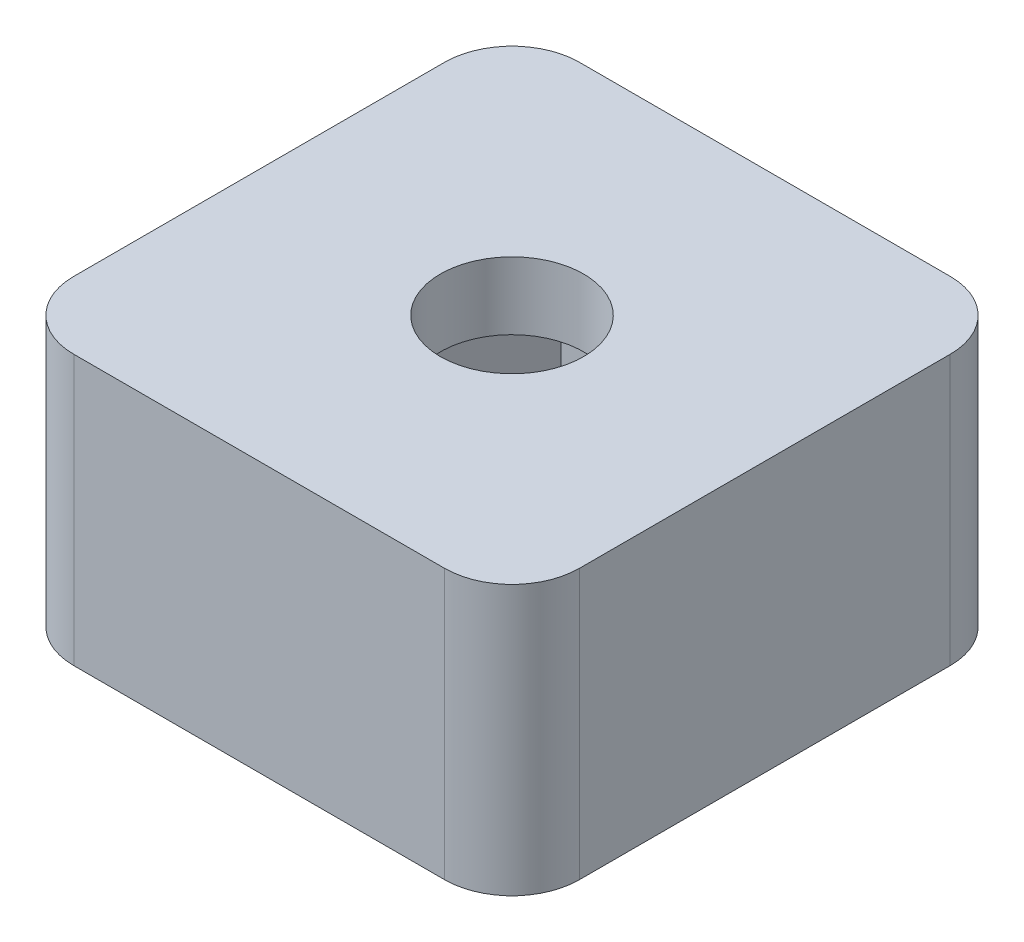
SolidWorks part; units mm, degrees
ref_plane "Front Plane" through (0, 0, 0) normal (0, 0, 1) x (1, 0, 0)
ref_plane "Top Plane" through (0, 0, 0) normal (0, 1, 0) x (1, 0, 0)
ref_plane "Right Plane" through (0, 0, 0) normal (1, 0, 0) x (0, 0, -1)
sketch "Sketch1" plane through (0, 0, 0) normal (0, 1, 0) x (1, 0, 0)
  line L1 (0, 0) -> (15, 0)
  line L2 (0, 0) -> (0, 15)
  line L3 (0, 15) -> (15, 15)
  line L4 (15, 0) -> (15, 15)
  dimension "D1" = 15
  dimension "D2" = 15
extrude "Boss-Extrude1" add sketch "Sketch1" along normal blind 8
sketch "Sketch3" plane through (0, 8, 0) normal (0, 1, 0) x (1, 0, 0)
  line L0 (15, 15) -> (0, 15) construction
  line L1 (0, 15) -> (0, 0) construction
  circle A0 centre (7.5, 7.5) radius 2.125
  point P2 (0, 0)
  point P5 (7.5, 15)
  point P8 (0, 7.5)
  dimension "D1" = 4.25
extrude "Cut-Extrude3" cut sketch "Sketch3" against normal through all
sketch "Sketch2" plane through (0, 0, 0) normal (0, 1, 0) x (1, 0, 0)
  line L5 (11.4837, 7.5) -> (9.4919, 10.95)
  line L6 (9.4919, 10.95) -> (5.5081, 10.95)
  line L7 (5.5081, 10.95) -> (3.5163, 7.5)
  line L8 (3.5163, 7.5) -> (5.5081, 4.05)
  line L9 (5.5081, 4.05) -> (9.4919, 4.05)
  line L10 (9.4919, 4.05) -> (11.4837, 7.5)
  circle A0 centre (7.5, 7.5) radius 3.45 construction
  circle A1 centre (7.5, 7.5) radius 2.125 construction
  point P0 (7.8263, 6.6128)
  dimension "D3" = 6.9
extrude "Cut-Extrude2" cut sketch "Sketch2" along normal blind 6
fillet "Fillet1" radius 2 4 edges at (15, 4, -15) (15, 4, 0) (0, 4, 0) (0, 4, -15)
